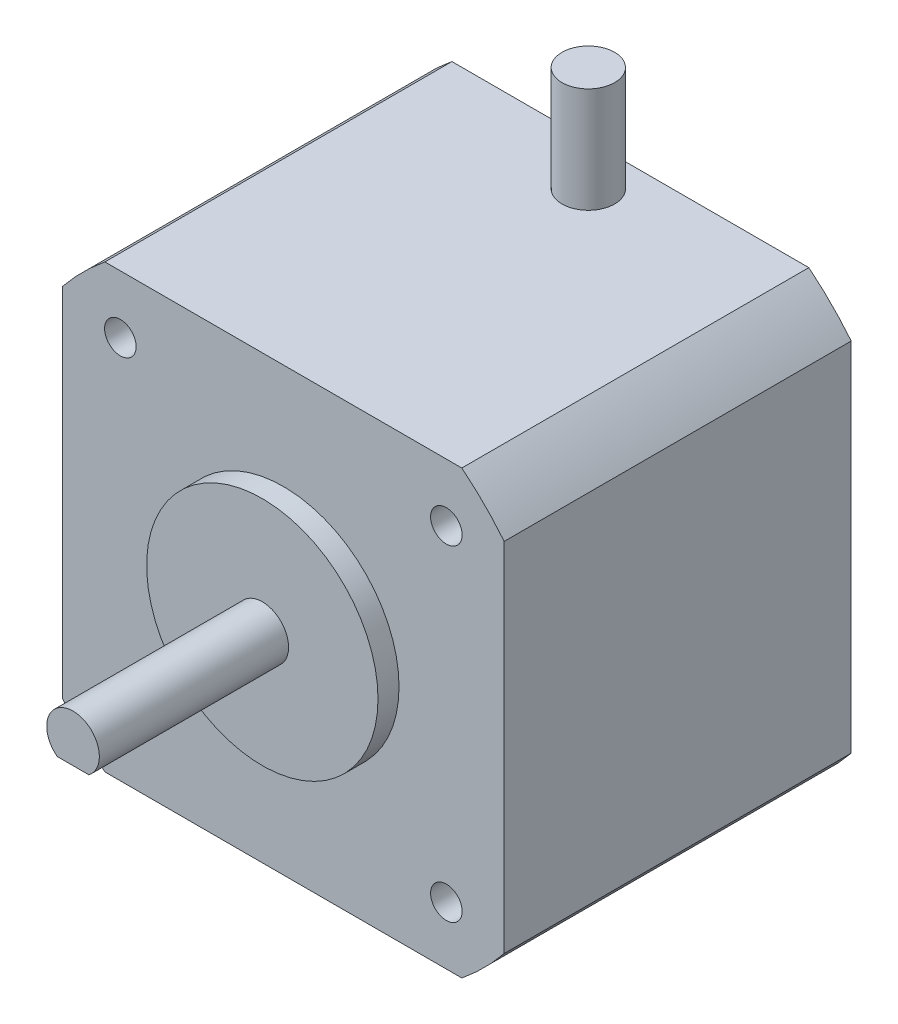
SolidWorks part; units mm, degrees
ref_plane "前基準面" through (0, 0, 0) normal (0, 0, 1) x (1, 0, 0)
ref_plane "上基準面" through (0, 0, 0) normal (0, 1, 0) x (1, 0, 0)
ref_plane "右基準面" through (0, 0, 0) normal (1, 0, 0) x (0, 0, -1)
sketch "草圖1" plane through (0, 0, 0) normal (0, 0, 1) x (1, 0, 0)
  line L1 (21, -21) -> (-21, -21)
  line L2 (21, -21) -> (21, 21)
  line L3 (21, 21) -> (-21, 21)
  line L4 (-21, -21) -> (-21, 21)
  line L5 (21, -21) -> (-21, 21) construction
  line L6 (21, 21) -> (-21, -21) construction
  point P0 (0, 0)
  dimension "D1" = 42
extrude "填料-伸長1" add sketch "草圖1" against normal blind 33
sketch "草圖2" plane through (0, 0, 0) normal (0, 0, 1) x (1, 0, 0)
  circle A0 centre (0, 0) radius 11
  dimension "D1" = 22
extrude "填料-伸長2" add sketch "草圖2" along normal blind 2
sketch "草圖3" plane through (0, 0, 2) normal (0, 0, 1) x (1, 0, 0)
  circle A0 centre (0, 0) radius 2.5
  dimension "D1" = 5
extrude "填料-伸長3" add sketch "草圖3" along normal blind 18
sketch "草圖4" plane through (0, 0, 20) normal (0, 0, 1) x (1, 0, 0)
  line L1 (1.5, -2) -> (-1.5, -2)
  circle A0 centre (0, 0) radius 2.5 construction
  arc A1 (-1.5, -2) -> (1.5, -2) centre (0, 0) ccw
  circle A3 centre (0, 0) radius 2.5 construction
  dimension "D1" = 4.5
extrude "除料-伸長2" cut sketch "草圖4" against normal up to surface (18 mm away) up to face at (2.5, 0, 2)
hole_wizard "M3 螺紋孔1" positions "草圖5" profile "草圖6" tap size "M3" standard "ISO"
sketch "草圖5" plane through (0, 0, 0) normal (0, 0, 1) x (1, 0, 0)
  line L1 (-15.5, 15.5) -> (0, 0) construction
  line L2 (0, 0) -> (-13.2283, 0) construction
  line L4 (0, 0) -> (0, 16.063) construction
  circle A0 centre (0, 0) radius 21.9203 construction
  point P0 (-15.5, 15.5)
  point P23 (15.5, 15.5)
  point P24 (15.5, -15.5)
  point P25 (-15.5, -15.5)
  dimension "D1" = 45
  dimension "D2" = 31
sketch "草圖6" plane through (-15.5, 15.5, 0) normal (1, 0, 0) x (0, -1, 0)
  line L0 (0, 0) -> (0, 8.2511)
  line L1 (0, 8.2511) -> (1.25, 7.5)
  line L2 (1.25, 7.5) -> (1.25, 6)
  line L3 (1.25, 6) -> (1.5, 6)
  line L4 (1.5, 6) -> (1.5, 0)
  line L5 (1.5, 0) -> (0, 0)
  line L10 (0, 8.2511) -> (-1.25, 7.5) construction
  line L11 (0, -6.35) -> (0, 107.95) construction
  dimension "螺孔鑽直徑" = 2.5
  dimension "螺孔鑽深度" = 7.5
  dimension "螺紋主直徑" = 3
  dimension "螺紋深度" = 6
  dimension "導頭角度" = 118
sketch "草圖7" plane through (0, 0, 0) normal (0, 0, 1) x (1, 0, 0)
  circle A0 centre (0, 0) radius 27
  dimension "D1" = 54
extrude "除料-伸長3" cut sketch "草圖7" against normal through all flip side to cut
sketch "草圖8" plane through (0, 21, 0) normal (0, 1, 0) x (1, 0, 0)
  line L0 (16.9706, 33) -> (-16.9706, 33) construction
  circle A0 centre (0, 29) radius 2.5
  point P2 (0, 0)
  dimension "D2" = 5
  dimension "D1" = 4
extrude "填料-伸長4" add sketch "草圖8" along normal blind 10
